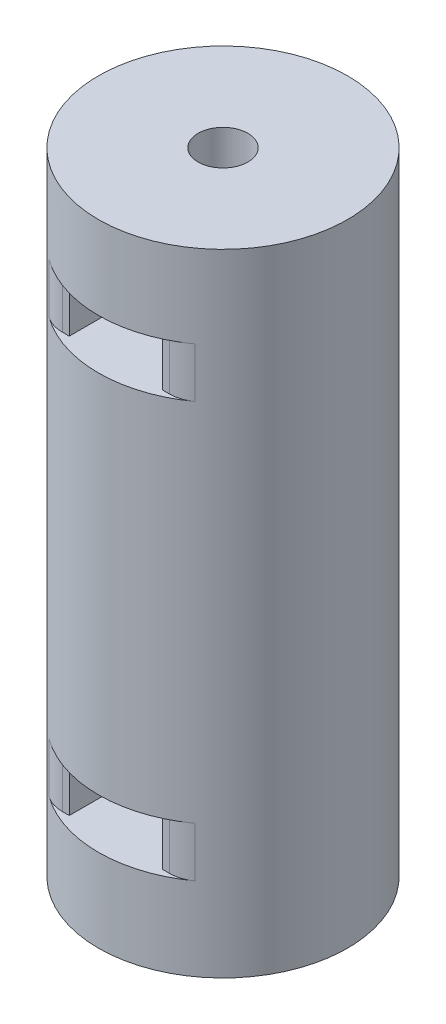
SolidWorks part; units mm, degrees
ref_plane "Front Plane" through (0, 0, 0) normal (0, 0, 1) x (1, 0, 0)
ref_plane "Top Plane" through (0, 0, 0) normal (0, 1, 0) x (1, 0, 0)
ref_plane "Right Plane" through (0, 0, 0) normal (1, 0, 0) x (0, 0, -1)
sketch "Sketch1" plane through (0, 0, 0) normal (0, 1, 0) x (1, 0, 0)
  circle A0 centre (0, 0) radius 1.5
  circle A1 centre (0, 0) radius 7.5
  dimension "D1" = 3
  dimension "D2" = 15
extrude "Boss-Extrude1" add sketch "Sketch1" along normal blind 38
ref_plane "Plane1" through (0, 33, 0) normal (0, 1, 0) x (1, 0, 0)
ref_plane "Plane2" through (0, 5, 0) normal (0, -1, 0) x (-1, 0, 0)
sketch "Sketch2" plane through (0, 33, 0) normal (0, 1, 0) x (1, 0, 0)
  line L1 (-2.8, -8.8823) -> (2.8, -8.8823)
  line L2 (-2.8, -8.8823) -> (-2.8, 8.8823)
  line L3 (-2.8, 8.8823) -> (2.8, 8.8823)
  line L4 (2.8, -8.8823) -> (2.8, 8.8823)
  line L5 (-2.8, -8.8823) -> (2.8, 8.8823) construction
  line L6 (-2.8, 8.8823) -> (2.8, -8.8823) construction
  point P0 (0, 0)
  dimension "D1" = 5.6
extrude "Cut-Extrude1" cut sketch "Sketch2" against normal blind 3
sketch "Sketch3" plane through (0, 5, 0) normal (0, -1, 0) x (-1, 0, 0)
  line L4 (-2.8, -8.8823) -> (2.8, -8.8823)
  line L5 (-2.8, 8.8823) -> (-2.8, -8.8823)
  line L6 (2.8, 8.8823) -> (-2.8, 8.8823)
  line L7 (2.8, -8.8823) -> (2.8, 8.8823)
  line L8 (-2.8, -8.8823) -> (2.8, -8.8823)
  line L9 (-2.8, 8.8823) -> (-2.8, -8.8823)
  line L10 (2.8, 8.8823) -> (-2.8, 8.8823)
  line L11 (2.8, -8.8823) -> (2.8, 8.8823)
  dimension "D1" = 0
extrude "Cut-Extrude2" cut sketch "Sketch3" against normal blind 3
sketch "Sketch4" plane through (0, 33, 0) normal (0, 1, 0) x (1, 0, 0)
  line L0 (0, 0) -> (12.9226, 0) construction
  line L1 (-2.8, -6.9577) -> (6.2487, -6.9577) construction
  line L2 (-2.8, -6.9577) -> (-2.8, -8.4897) construction
  line L3 (-2.8, -8.4897) -> (6.2487, -8.4897) construction
  line L4 (6.2487, -6.9577) -> (6.2487, -8.4897) construction
  line L5 (-2.8, 6.9577) -> (-2.8, 8.4897) construction
  line L6 (-2.8, 8.4897) -> (6.2487, 8.4897) construction
  line L7 (6.2487, 6.9577) -> (6.2487, 8.4897) construction
  line L8 (-2.8, 6.9577) -> (6.2487, 6.9577) construction
  line L10 (-13.4291, 13.9623) -> (15.1348, 13.9623)
  line L11 (-13.4291, 13.9623) -> (-13.4291, 6.4577)
  line L12 (-13.4291, 6.4577) -> (15.1348, 6.4577)
  line L13 (15.1348, 13.9623) -> (15.1348, 6.4577)
  line L14 (12.7205, -12.7406) -> (-10.8112, -12.7406)
  line L15 (12.7205, -12.7406) -> (12.7205, -6.4577)
  line L16 (12.7205, -6.4577) -> (-10.8112, -6.4577)
  line L17 (-10.8112, -12.7406) -> (-10.8112, -6.4577)
  arc A0 (-2.8, -6.9577) -> (2.8, -6.9577) centre (0, 0) ccw construction
  arc A1 (-2.8, -6.9577) -> (2.8, -6.9577) centre (0, 0) ccw construction
  dimension "D1" = 0.5
  dimension "D2" = 0.5
extrude "Cut-Extrude3" cut sketch "Sketch4" against normal blind 3
sketch "Sketch5" plane through (0, 5, 0) normal (0, -1, 0) x (-1, 0, 0)
  line L4 (13.4291, 13.9623) -> (-15.1348, 13.9623)
  line L5 (-15.1348, 13.9623) -> (-15.1348, 6.4577)
  line L6 (-15.1348, 6.4577) -> (13.4291, 6.4577)
  line L7 (13.4291, 6.4577) -> (13.4291, 13.9623)
  line L8 (13.4291, 13.9623) -> (-15.1348, 13.9623)
  line L9 (-15.1348, 13.9623) -> (-15.1348, 6.4577)
  line L10 (-15.1348, 6.4577) -> (13.4291, 6.4577)
  line L11 (13.4291, 6.4577) -> (13.4291, 13.9623)
  line L12 (-12.7205, -12.7406) -> (10.8112, -12.7406)
  line L13 (-12.7205, -6.4577) -> (-12.7205, -12.7406)
  line L14 (10.8112, -6.4577) -> (-12.7205, -6.4577)
  line L15 (10.8112, -12.7406) -> (10.8112, -6.4577)
  line L16 (-12.7205, -12.7406) -> (10.8112, -12.7406)
  line L17 (-12.7205, -6.4577) -> (-12.7205, -12.7406)
  line L18 (10.8112, -6.4577) -> (-12.7205, -6.4577)
  line L19 (10.8112, -12.7406) -> (10.8112, -6.4577)
  dimension "D1" = 0
  dimension "D2" = 0
extrude "Cut-Extrude4" cut sketch "Sketch5" against normal blind 3
fillet "Fillet1" radius 2 8 edges at (-3.8141, 6.5, -6.4577) (3.8141, 6.5, -6.4577) (3.8141, 31.5, -6.4577) (-3.8141, 31.5, -6.4577) (-3.8141, 31.5, 6.4577) (3.8141, 31.5, 6.4577) (3.8141, 6.5, 6.4577) (-3.8141, 6.5, 6.4577)
